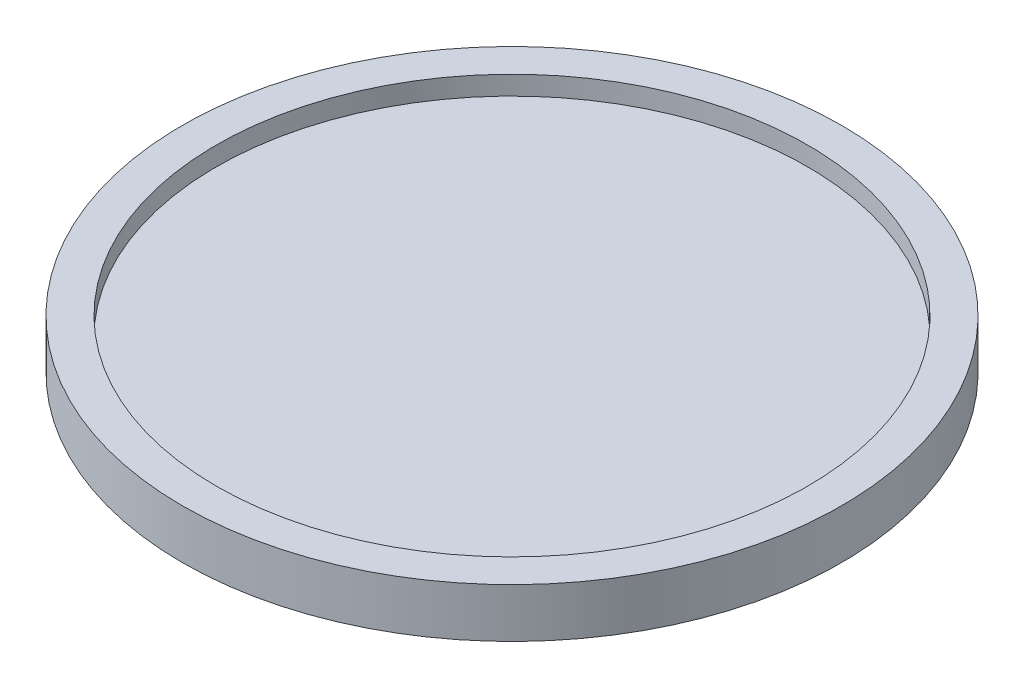
SolidWorks part; units mm, degrees
ref_plane "Alzado" through (0, 0, 0) normal (0, 0, 1) x (1, 0, 0)
ref_plane "Planta" through (0, 0, 0) normal (0, 1, 0) x (1, 0, 0)
ref_plane "Vista lateral" through (0, 0, 0) normal (1, 0, 0) x (0, 0, -1)
sketch "Croquis1" plane through (0, 0, 0) normal (0, 1, 0) x (1, 0, 0)
  circle A0 centre (0, 0) radius 43.5
  dimension "D1" = 87
extrude "Saliente-Extruir1" add sketch "Croquis1" along normal blind 4
sketch "Croquis2" plane through (0, 4, 0) normal (0, 1, 0) x (1, 0, 0)
  circle A0 centre (0, 0) radius 43.5
  circle A1 centre (0, 0) radius 39.0179
extrude "Saliente-Extruir2" add sketch "Croquis2" along normal blind 2.5
sketch "Croquis3" plane through (0, 0, 0) normal (0, -1, 0) x (1, 0, 0)
  circle A0 centre (0, 0) radius 38.311
  circle A1 centre (0, 0) radius 33.6043
extrude "Saliente-Extruir3" add sketch "Croquis3" along normal blind 2.5
